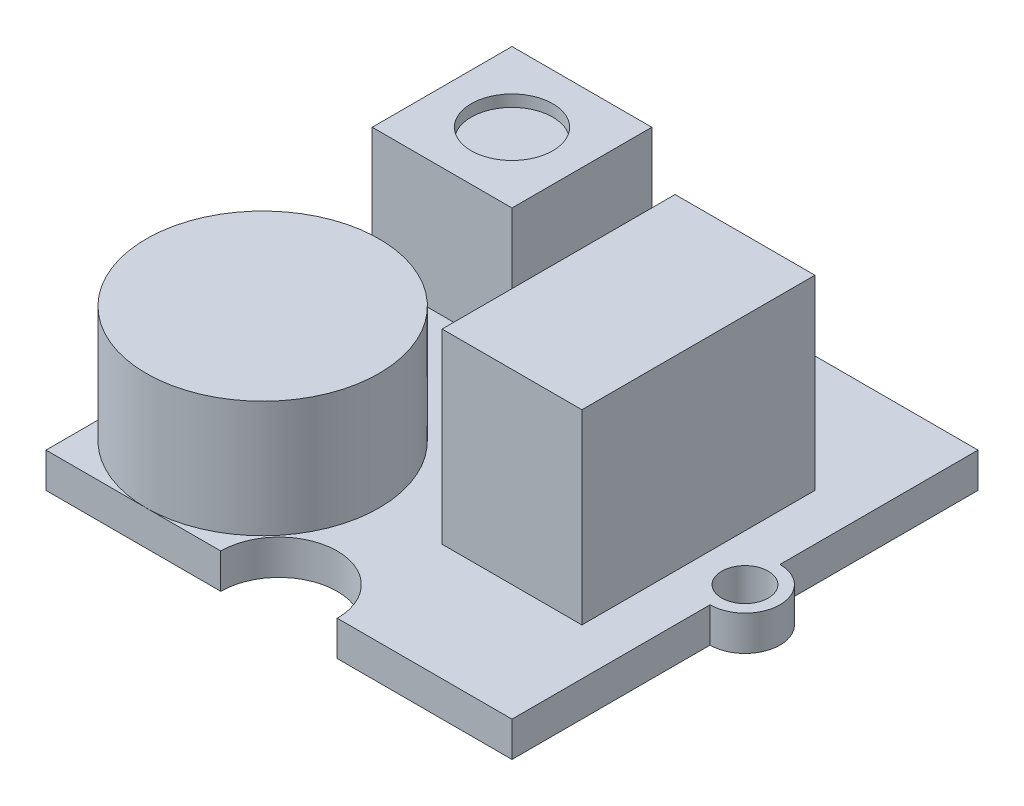
SolidWorks part; units mm, degrees
ref_plane "Front Plane" through (0, 0, 0) normal (0, 0, 1) x (1, 0, 0)
ref_plane "Top Plane" through (0, 0, 0) normal (0, 1, 0) x (1, 0, 0)
ref_plane "Right Plane" through (0, 0, 0) normal (1, 0, 0) x (0, 0, -1)
sketch "Sketch1" plane through (0, 0, 0) normal (0, 1, 0) x (1, 0, 0)
  line L1 (-10, 10) -> (10, 10)
  line L2 (-10, 10) -> (-10, -10)
  line L3 (-10, -10) -> (10, -10)
  line L4 (10, 10) -> (10, -10)
  line L5 (-10, 10) -> (10, -10) construction
  line L6 (-10, -10) -> (10, 10) construction
  point P0 (0, 0)
  dimension "D1" = 20
  dimension "D2" = 20
extrude "Boss-Extrude1" add sketch "Sketch1" along normal blind 1.5
sketch "Sketch2" plane through (0, 1.5, 0) normal (0, 1, 0) x (1, 0, 0)
  line L0 (-10, 10) -> (-10, -10) construction
  line L1 (10, -10) -> (10, 10) construction
  circle A0 centre (-10, 0) radius 1.5
  circle A1 centre (10, 0) radius 1.5
  dimension "D1" = 3
  dimension "D2" = 3
extrude "Boss-Extrude2" add sketch "Sketch2" against normal blind 1.5
sketch "Sketch3" plane through (0, 1.5, 0) normal (0, 1, 0) x (1, 0, 0)
  line L0 (10, 10) -> (-10, 10) construction
  line L1 (-10, -10) -> (10, -10) construction
  circle A0 centre (-10, 0) radius 1
  circle A1 centre (10, 0) radius 1
  circle A2 centre (0, 10) radius 2.5
  circle A3 centre (0, -10) radius 2.5
  dimension "D1" = 2
  dimension "D2" = 2
  dimension "D3" = 5
  dimension "D4" = 5
extrude "Cut-Extrude1" cut sketch "Sketch3" against normal blind 1.5
sketch "Sketch4" plane through (0, 1.5, 0) normal (0, 1, 0) x (1, 0, 0)
  line L0 (-10, -10) -> (-2.5, -10) construction
  line L1 (-10, -1.5) -> (-10, -10) construction
  circle A0 centre (-5.7, -5) radius 5
  dimension "D1" = 10
  dimension "D2" = 5
  dimension "D3" = 4.3
extrude "Boss-Extrude3" add sketch "Sketch4" along normal blind 5
sketch "Sketch5" plane through (0, 1.5, 0) normal (0, 1, 0) x (1, 0, 0)
  line L0 (-2.5, 10) -> (-10, 10) construction
  line L1 (-9.5, 9.5) -> (-3.5, 9.5)
  line L2 (-9.5, 9.5) -> (-9.5, 3.5)
  line L3 (-9.5, 3.5) -> (-3.5, 3.5)
  line L4 (-3.5, 9.5) -> (-3.5, 3.5)
  line L5 (-9.5, 9.5) -> (-3.5, 3.5) construction
  line L6 (-9.5, 3.5) -> (-3.5, 9.5) construction
  line L7 (-10, 10) -> (-10, 1.5) construction
  point P0 (-6.5, 6.5)
  dimension "D1" = 6
  dimension "D2" = 6
  dimension "D3" = 0.5
  dimension "D4" = 0.5
extrude "Boss-Extrude4" add sketch "Sketch5" along normal blind 5.5
sketch "Sketch6" plane through (0, 1.5, 0) normal (0, 1, 0) x (1, 0, 0)
  line L0 (10, 1.5) -> (10, 10) construction
  line L1 (2, 5) -> (8, 5)
  line L2 (2, 5) -> (2, -5)
  line L3 (2, -5) -> (8, -5)
  line L4 (8, 5) -> (8, -5)
  line L5 (2, 5) -> (8, -5) construction
  line L6 (2, -5) -> (8, 5) construction
  line L7 (10, 10) -> (2.5, 10) construction
  point P0 (5, 0)
  dimension "D1" = 6
  dimension "D2" = 10
  dimension "D3" = 2
  dimension "D4" = 5
extrude "Boss-Extrude5" add sketch "Sketch6" along normal blind 8
sketch "Sketch7" plane through (0, 1.5, 0) normal (0, 1, 0) x (1, 0, 0)
  line L0 (-10, 10) -> (-10, 1.5) construction
  line L1 (-2, 5.203) -> (1, 5.203)
  line L2 (-2, 5.203) -> (-2, 3.3829)
  line L3 (-2, 3.3829) -> (1, 3.3829)
  line L4 (1, 5.203) -> (1, 3.3829)
  line L5 (-2, 5.203) -> (1, 3.3829) construction
  line L6 (-2, 3.3829) -> (1, 5.203) construction
  point P0 (-0.5, 4.293)
  dimension "D1" = 3
  dimension "D2" = 1.8201
  dimension "D3" = 8
extrude "Boss-Extrude6" add sketch "Sketch7" along normal blind 1
sketch "Sketch8" plane through (0, 7, 0) normal (0, 1, 0) x (1, 0, 0)
  line L0 (-9.5, 9.5) -> (-9.5, 3.5) construction
  line L1 (-3.5, 9.5) -> (-9.5, 9.5) construction
  circle A0 centre (-6.5, 6.5) radius 1.75
  dimension "D2" = 3
  dimension "D3" = 3.5
  dimension "D1" = 3
extrude "Cut-Extrude2" cut sketch "Sketch8" against normal blind 0.5
